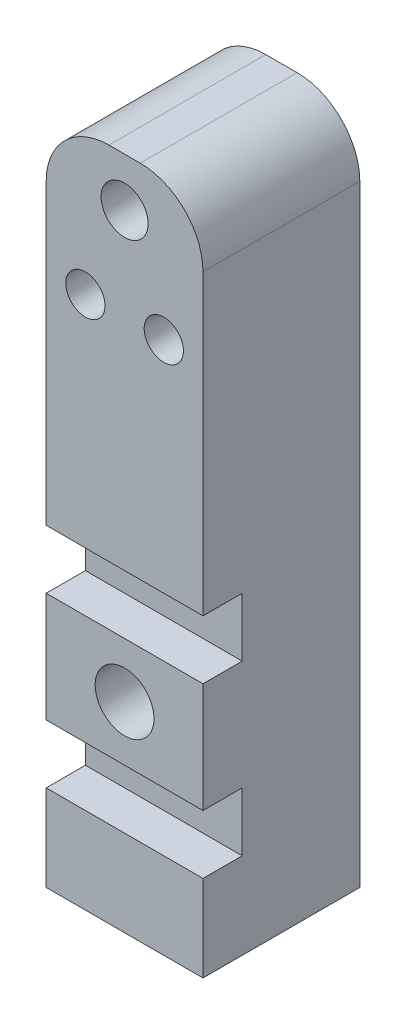
SolidWorks part; units mm, degrees
ref_plane "Front Plane" through (0, 0, 0) normal (0, 0, 1) x (1, 0, 0)
ref_plane "Top Plane" through (0, 0, 0) normal (0, 1, 0) x (1, 0, 0)
ref_plane "Right Plane" through (0, 0, 0) normal (1, 0, 0) x (0, 0, -1)
sketch "Sketch1" plane through (0, 0, 0) normal (0, 0, 1) x (1, 0, 0)
  line L0 (0, 21.5) -> (0, 18.4) construction
  line L1 (-5, 21.5) -> (5, 21.5)
  line L2 (-5, 21.5) -> (-5, -21.5)
  line L3 (-5, -21.5) -> (5, -21.5)
  line L4 (5, 21.5) -> (5, -21.5)
  line L5 (0, 21.5) -> (0, 12.5) construction
  line L6 (0, -21.5) -> (0, -5.25) construction
  line L7 (-5, -5.25) -> (5, -5.25)
  line L8 (0, -5.25) -> (0, -1.5) construction
  line L9 (-5, -1.5) -> (5, -1.5)
  line L10 (0, -21.5) -> (0, -8.75) construction
  line L11 (0, -8.75) -> (5, -8.75) construction
  line L12 (-5, -12.25) -> (5, -12.25)
  line L13 (-5, -16) -> (5, -16)
  circle A0 centre (0, 18.4) radius 1.5
  circle A1 centre (-2.5, 12.5) radius 1.25
  circle A2 centre (2.5, 12.5) radius 1.25
  circle A3 centre (0, -8.75) radius 1.875
  point P0 (0, 0)
  point P19 (0, -5.25)
  point P22 (0, -1.5)
  dimension "D4" = 3
  dimension "D7" = 2.5
  dimension "D11" = 3.75
  dimension "D1" = 43
  dimension "D2" = 10
  dimension "D3" = 3.1
  dimension "D5" = 9
  dimension "D6" = 2.5
  dimension "D8" = 16.25
  dimension "D9" = 3.75
  dimension "D10" = 12.75
extrude "Boss-Extrude1" add sketch "Sketch1" along normal blind 10 contours L2 L9 L4 L1 A0 A1 A2 | L2 L12 L4 L7 A3 | L13 L2 L3 L4
fillet "Fillet1" radius 4 2 edges at (-5, 21.5, 5) (5, 21.5, 5)
sketch "Sketch2" plane through (0, 0, 0) normal (0, 0, -1) x (-1, 0, 0)
  circle A0 centre (0, 18.4) radius 1.5363
extrude "Boss-Extrude3" add sketch "Sketch2" against normal blind 3.5
sketch "Sketch3" plane through (0, 0, 0) normal (0, 0, -1) x (-1, 0, 0)
  line L1 (-5, -1.3295) -> (5, -1.3295)
  line L2 (-5, -1.3295) -> (-5, -5.25)
  line L3 (-5, -5.25) -> (5, -5.25)
  line L4 (5, -1.3295) -> (5, -5.25)
  line L5 (-5, -1.3295) -> (5, -5.25) construction
  line L6 (-5, -5.25) -> (5, -1.3295) construction
  point P0 (0, -3.2897)
extrude "Boss-Extrude4" add sketch "Sketch3" against normal blind 7.5
sketch "Sketch4" plane through (0, 0, 0) normal (0, 0, -1) x (-1, 0, 0)
  line L1 (-5, -12.226) -> (5, -12.226)
  line L2 (-5, -12.226) -> (-5, -16)
  line L3 (-5, -16) -> (5, -16)
  line L4 (5, -12.226) -> (5, -16)
  line L5 (-5, -12.226) -> (5, -16) construction
  line L6 (-5, -16) -> (5, -12.226) construction
  point P0 (0, -14.113)
extrude "Boss-Extrude5" add sketch "Sketch4" against normal blind 7.5
sketch "Sketch5" plane through (0, -21.5, 0) normal (0, -1, 0) x (1, 0, 0)
  line L0 (0, 0) -> (0, 5) construction
  circle A0 centre (0, 5) radius 1
  dimension "D2" = 2
  dimension "D1" = 5
extrude "Cut-Extrude1" cut sketch "Sketch5" against normal blind 7
